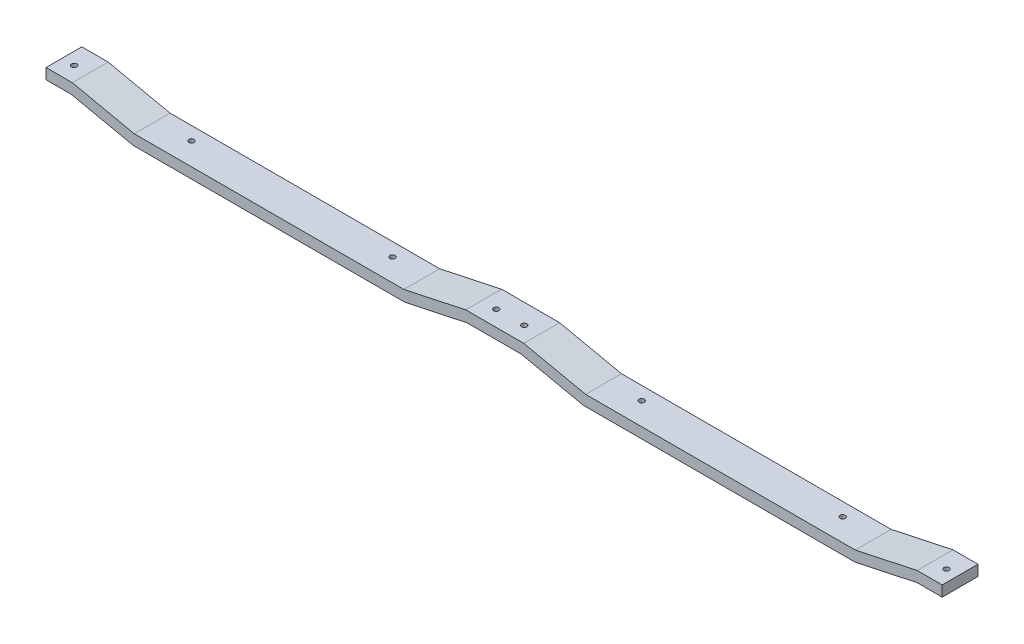
SolidWorks part; units mm, degrees
ref_plane "Front Plane" through (0, 0, 0) normal (0, 0, 1) x (1, 0, 0)
ref_plane "Top Plane" through (0, 0, 0) normal (0, 1, 0) x (1, 0, 0)
ref_plane "Right Plane" through (0, 0, 0) normal (1, 0, 0) x (0, 0, -1)
sketch "Sketch1" plane through (0, 0, 0) normal (0, 0, 1) x (1, 0, 0)
  line L0 (-37.2967, 0.25) -> (-37.2967, -57.3811)
  line L13 (37.2967, 0.25) -> (47.5467, 0.25)
  line L15 (48.0084, 2.25) -> (37.085, 2.25)
  line L17 (25.4085, -0.25) -> (-25.4087, -0.25)
  line L19 (-37.085, 2.25) -> (-42.05, 2.25)
  line L20 (-42.05, 2.25) -> (-42.05, 0.25)
  line L21 (-42.05, 0.25) -> (-37.2967, 0.25)
  line L23 (-25.6204, -2.25) -> (25.6202, -2.25)
  line L24 (-37.2967, 0.25) -> (-25.6204, -2.25)
  line L26 (25.4085, -0.25) -> (37.085, 2.25)
  line L27 (-25.4087, -0.25) -> (-37.085, 2.25)
  line L29 (25.6202, -2.25) -> (37.2967, 0.25)
  line L47 (59.2232, -2.25) -> (47.5467, 0.25)
  line L48 (110.5022, -0.25) -> (122.1785, 2.25)
  line L49 (59.6849, -0.25) -> (48.0084, 2.25)
  line L50 (122.1402, 0.25) -> (110.4639, -2.25)
  line L51 (110.4639, -2.25) -> (59.2232, -2.25)
  line L52 (126.8935, 0.25) -> (122.1402, 0.25)
  line L53 (126.8935, 2.25) -> (126.8935, 0.25)
  line L54 (122.1785, 2.25) -> (126.8935, 2.25)
  line L55 (59.6849, -0.25) -> (110.5022, -0.25)
  point P12 (-25.4087, 4.9059)
  point P19 (-25.4087, 2.25)
  point P23 (-23.5553, 3.2698)
  dimension "D2" = 4.965
  dimension "D3" = 37.085
  dimension "D1" = 10.25
  dimension "D4" = 37.2967
  dimension "D5" = 48.0084
  dimension "D6" = 59.2232
  dimension "D7" = 110.4639
  dimension "D8" = 110.5022
  dimension "D9" = 122.1402
  dimension "D10" = 25.6204
  dimension "D11" = 0.25
  dimension "D12" = 2.25
  dimension "D13" = 0.25
  dimension "D14" = 2.25
extrude "Boss-Extrude1" add sketch "Sketch1" along normal blind 6.75 contours L21 L24 L23 L29 L13 L47 L51 L50 L52 L53 L54 L48 L55 L49 L15 L26 L17 L27 L19 L20
sketch "Sketch2" plane through (0, -0.25, 0) normal (0, 1, 0) x (1, 0, 0)
  line L0 (-25.4087, -6.75) -> (-25.4087, 0) construction
  line L1 (42.5467, 0) -> (42.5467, -6.75) construction
  line L2 (-39.7369, -3.7605) -> (39.8631, -3.7605) construction
  line L3 (25.4085, 0) -> (-25.4087, 0) construction
  line L4 (48.0084, 0) -> (37.085, 0) construction
  line L5 (48.0084, -6.75) -> (37.085, -6.75) construction
  line L6 (19.039, -2.5147) -> (-18.8564, -2.5147) construction
  circle A0 centre (45.1131, -3.7605) radius 0.5
  circle A1 centre (65.9936, -2.5147) radius 0.5
  circle A2 centre (103.889, -2.5147) radius 0.5
  circle A3 centre (124.7131, -3.7605) radius 0.5
  circle A6 centre (39.8631, -3.7605) radius 0.5
  circle A8 centre (-39.7369, -3.7605) radius 0.5
  circle A10 centre (19.039, -2.5147) radius 0.5
  circle A12 centre (-18.8564, -2.5147) radius 0.5
  dimension "D1" = 1
  dimension "D2" = 6.5523
  dimension "D3" = 44.4477
  dimension "D5" = 70.5218
  dimension "D4" = 65.2718
  dimension "D6" = 91.4023
  dimension "D7" = 129.2977
  dimension "D8" = 150.1218
  dimension "D9" = 14.3282
  dimension "D10" = 2.5147
  dimension "D11" = 3.7605
extrude "Cut-Extrude1" cut sketch "Sketch2" against normal through all both and the other way through all
